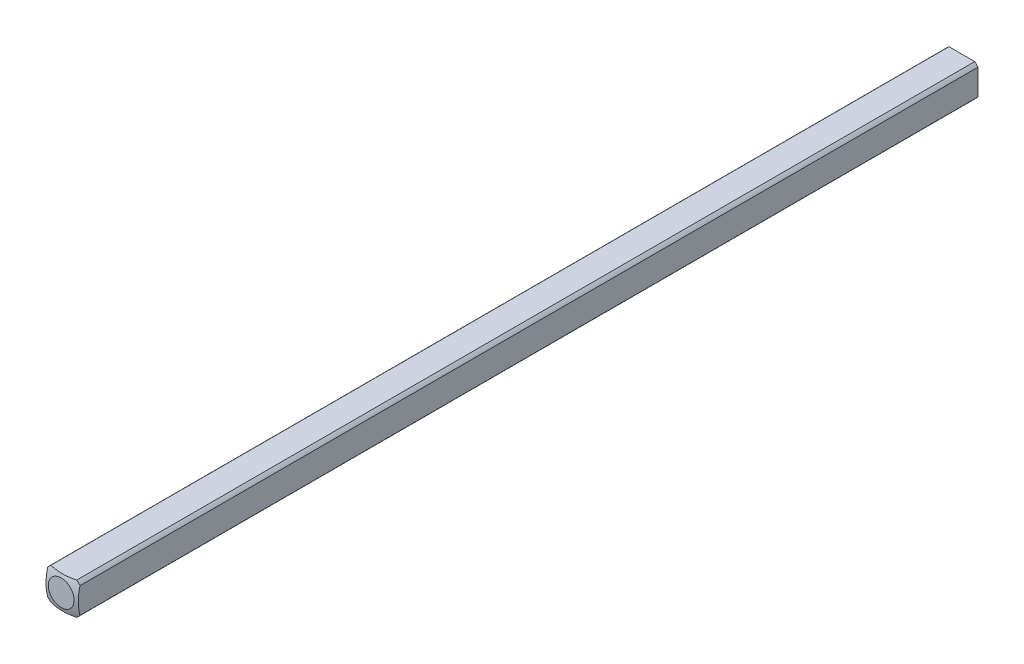
SolidWorks part; units mm, degrees
material "Custom Plastic"
ref_plane "Front Plane" through (0, 0, 0) normal (0, 0, 1) x (1, 0, 0)
ref_plane "Top Plane" through (0, 0, 0) normal (0, 1, 0) x (1, 0, 0)
ref_plane "Right Plane" through (0, 0, 0) normal (1, 0, 0) x (0, 0, -1)
sketch "Sketch1" plane through (0, 0, 0) normal (0, 0, 1) x (1, 0, 0)
  line L0 (-1.5875, -1.5875) -> (1.5875, 1.5875) construction
  line L1 (-1.5875, -1.5875) -> (1.5875, -1.5875)
  line L2 (-1.5875, -1.5875) -> (-1.5875, 1.5875)
  line L3 (-1.5875, 1.5875) -> (1.5875, 1.5875)
  line L4 (1.5875, -1.5875) -> (1.5875, 1.5875)
  dimension "D1" = 3.175
extrude "Boss-Extrude1" add sketch "Sketch1" along normal blind 152.4
sketch "Sketch2" plane through (0, 0, 0) normal (0, 0, -1) x (-1, 0, 0)
  circle A0 centre (0, 0) radius 2.032
  dimension "D1" = 4.064
extrude "Cut-Extrude1" cut sketch "Sketch2" against normal through all flip side to cut
ref_axis "Axis1" through (0, 0, 152.4) along (0, 0, -1)
sketch "Sketch3" plane through (0, 0, 0) normal (0, 1, 0) x (1, 0, 0)
  line L1 (-5.0537, -4.4027) -> (-5.0537, 5.7405)
  line L2 (-5.0537, 5.7405) -> (0, 5.7405)
  line L5 (0, -152.4) -> (0, 0) construction
  line L8 (0, 0.1609) -> (0, 5.7405)
  arc A0 (-5.0537, -4.4027) -> (0, 0.1609) centre (0, -4.9191) cw
  dimension "D1" = 5.08
revolve "Cut-Revolve1" cut sketch "Sketch3" angle 360 about axis through (0, 0, 152.4) along (0, 0, -1)
mirror "Mirror1" about plane through (0, 0, 152.4) normal (0, 0, -1) of bodies 103
sketch "Sketch4" plane through (1.5875, 0, 0) normal (1, 0, 0) x (0, 0, -1)
  line L1 (-0.2632, -1.5875) -> (-203.4632, -1.5875)
  line L2 (-0.2632, 1.5875) -> (-203.4632, 1.5875)
  line L3 (-203.4632, -1.5875) -> (-203.4632, 1.5875)
  line L4 (-0.2632, -1.5875) -> (0.8357, -1.5875)
  line L5 (0.8357, -1.5875) -> (0.8357, 1.5875)
  line L6 (0.8357, 1.5875) -> (-0.2632, 1.5875)
  dimension "D1" = 203.2
extrude "Cut-Extrude2" cut sketch "Sketch4" against normal through all
sketch "Sketch6" plane through (0, -1.5875, 0) normal (0, -1, 0) x (1, 0, 0)
  line L0 (1.5875, 203.4632) -> (1.5875, 216.1632)
  line L1 (1.5875, 203.4632) -> (1.5875, 304.5368) construction
  line L2 (1.5875, 216.1632) -> (-1.5875, 216.1632)
  line L3 (-1.5875, 304.5368) -> (-1.5875, 203.4632) construction
  line L4 (-1.5875, 216.1632) -> (-1.5875, 203.4632)
  line L5 (-1.5875, 203.4632) -> (1.5875, 203.4632)
  dimension "D1" = 12.7
extrude "Cut-Extrude3" cut sketch "Sketch6" against normal through all
